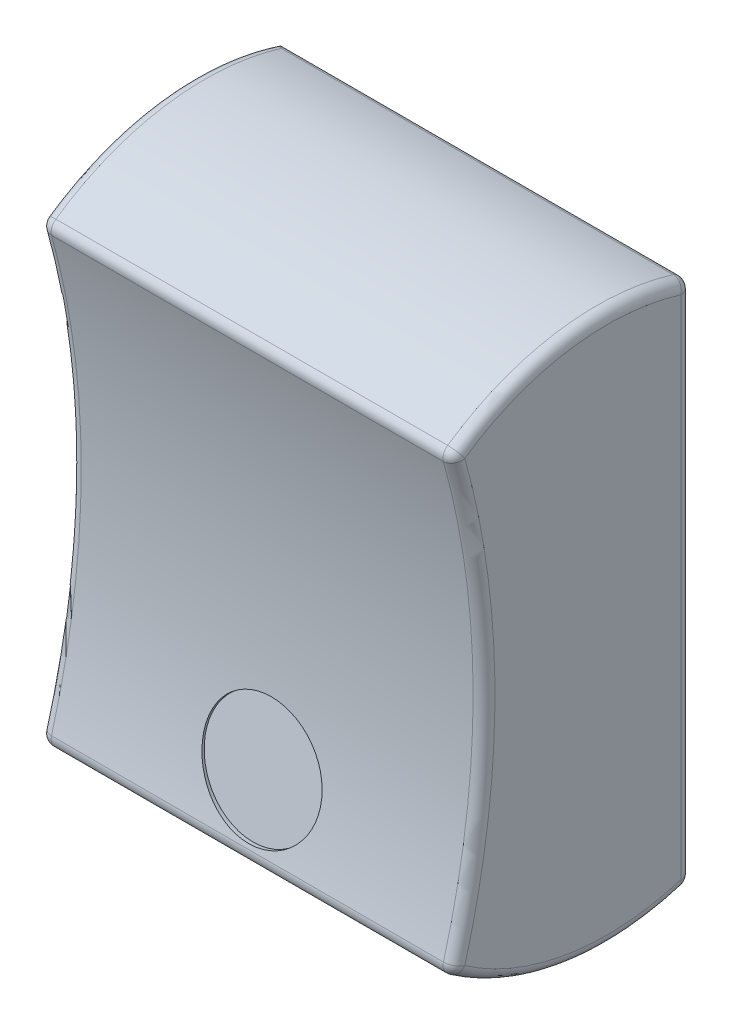
SolidWorks part; units mm, degrees
ref_plane "Front Plane" through (0, 0, 0) normal (0, 0, 1) x (1, 0, 0)
ref_plane "Top Plane" through (0, 0, 0) normal (0, 1, 0) x (1, 0, 0)
ref_plane "Right Plane" through (0, 0, 0) normal (1, 0, 0) x (0, 0, -1)
sketch "Sketch2" plane through (0, 0, 0) normal (1, 0, 0) x (0, 0, -1)
  line L0 (0, 12) -> (0, -12)
  arc A0 (-11, -10.29) -> (-11, 10.29) centre (-46.5403, 0) ccw
  arc A3 (-11, 10.29) -> (0, 12) centre (-3.867, 0.6401) cw
  arc A4 (-11, -10.29) -> (0, -12) centre (-3.867, -0.6401) ccw
  point P4 (0, 0)
  dimension "D2" = 12
  dimension "D3" = 37
  dimension "D1" = 20.58
  dimension "D4" = 24
  dimension "D5" = 11
extrude "Boss-Extrude2" add sketch "Sketch2" along normal mid plane 19
fillet "Fillet1" radius 0.5 11 edges at (0, -12, 0) (0, -10.29, 11) (-9.5, -12.4977, 5.7103) (9.5, -12.4977, 5.7103) (9.5, 0, 0) (0, 12, 0) (0, 10.29, 11) (9.5, 12.4977, 5.7103) (-9.5, 12.4977, 5.7103) (-9.5, 0, 9.5403) (9.5, 0, 9.5403)
ref_plane "Plane1" through (0, 1.6572, 8.5257) normal (0, 0.1908, 0.9816) x (-1, 0, 0)
sketch "Sketch3" plane through (0, 1.6572, 8.5257) normal (0, 0.1908, 0.9816) x (-1, 0, 0)
  circle A0 centre (0, 8.948) radius 2.71
  dimension "D1" = 5.42
extrude "Cut-Extrude1" cut sketch "Sketch3" against normal blind 0.1 and the other way through all
